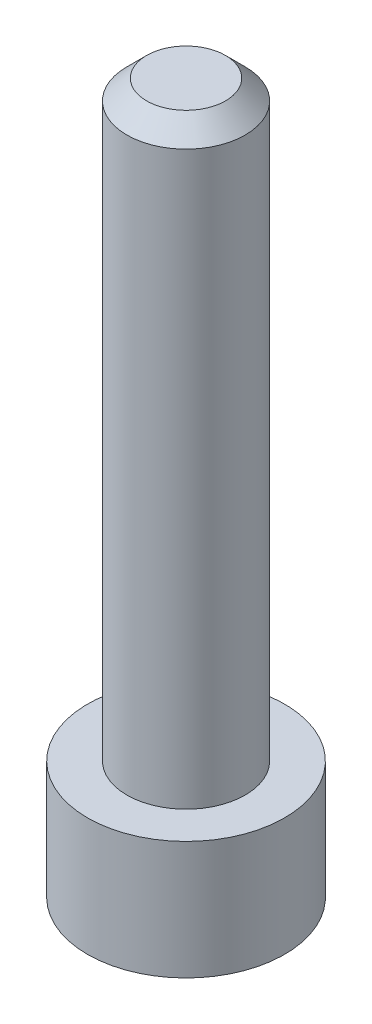
SolidWorks part; units mm, degrees
ref_plane "Plan de face" through (0, 0, 0) normal (0, 0, 1) x (1, 0, 0)
ref_plane "Plan de dessus" through (0, 0, 0) normal (0, 1, 0) x (1, 0, 0)
ref_plane "Plan de droite" through (0, 0, 0) normal (1, 0, 0) x (0, 0, -1)
sketch "Esquisse1" plane through (0, 0, 0) normal (0, 0, 1) x (1, 0, 0)
  line L0 (0, 0) -> (1.5, 0)
  line L1 (1.5, 0) -> (1.5, -15)
  line L2 (1.5, -15) -> (2.5, -15)
  line L3 (2.5, -15) -> (2.5, -18)
  line L4 (2.5, -18) -> (0, -18)
  line L5 (0, 0) -> (0, -4.6949) construction
  line L6 (0, 0) -> (0, -18)
  dimension "D1" = 15
  dimension "D2" = 3
  dimension "D3" = 1.5
  dimension "D4" = 2.5
revolve "Révolution1" add sketch "Esquisse1" angle 360 about L5
chamfer "Chanfrein1" distance 0.5 angle 45 1 edges at (0, 0, 1.5)
